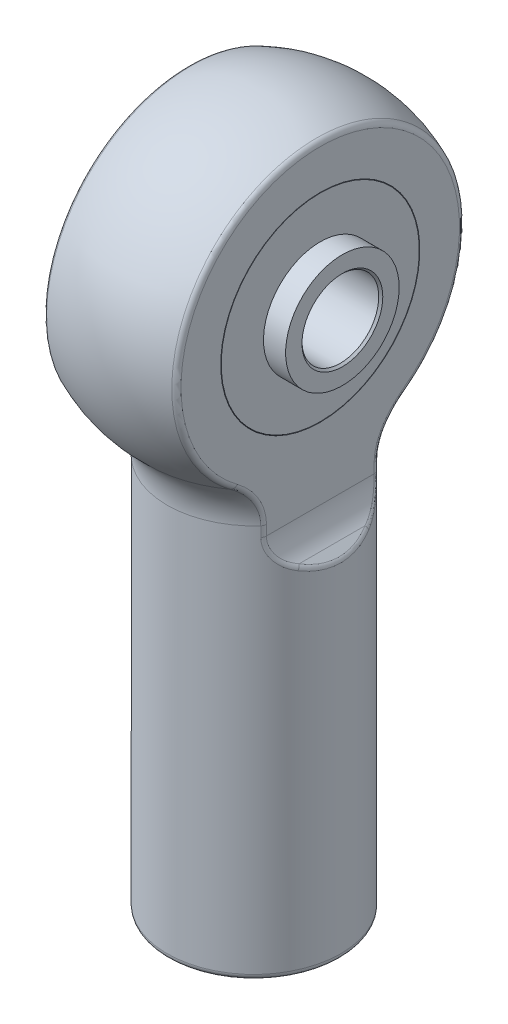
SolidWorks part; units mm, degrees
other "C-Rev Ball"
other "C-Rev Body"
material "AISI 1020"
ref_plane "Front Plane" through (0, 0, 0) normal (0, 0, 1) x (1, 0, 0)
ref_plane "Top Plane" through (0, 0, 0) normal (0, 1, 0) x (1, 0, 0)
ref_plane "Right Plane" through (0, 0, 0) normal (1, 0, 0) x (0, 0, -1)
sketch "Sketch1" plane through (0, 0, 0) normal (0, 0, 1) x (1, 0, 0)
  line L0 (0, 0) -> (0, -34.925) construction
  line L1 (-3.4544, -34.925) -> (-5.461, -34.925)
  line L2 (-5.461, -34.925) -> (-5.461, -8.28)
  line L3 (0, -10.8633) -> (0, 9.9187)
  line L4 (0, -10.8633) -> (-3.4544, -12.7)
  line L5 (-3.4544, -12.7) -> (-3.4544, -34.925)
  arc A0 (0, 9.9187) -> (-5.461, -8.28) centre (0, 0) ccw
  dimension "D2" = 19.8374
  dimension "D1" = 34.925
  dimension "D3" = 10.922
  dimension "D4" = 22.225
  dimension "D7" = 118
  dimension "D8" = 6.9088
revolve "Revolve1" add sketch "Sketch1" angle 360 about L0
sketch "Sketch2" plane through (0, 0, 0) normal (0, 0, 1) x (1, 0, 0)
  line L0 (0, 0) -> (0, 10.8779) construction
  line L1 (4.1656, 9.0016) -> (4.1656, -10.7585)
  line L2 (-4.1656, 9.0016) -> (-4.1656, -10.7585)
  line L4 (-4.9095, -12.5545) -> (-5.461, -13.106)
  line L5 (-5.461, -8.28) -> (-5.461, -34.925) construction
  line L6 (-5.461, -8.28) -> (-5.461, -13.106)
  line L7 (4.9095, -12.5545) -> (5.461, -13.106)
  line L8 (5.461, -8.28) -> (5.461, -13.106)
  arc A0 (5.461, -8.28) -> (-5.461, -8.28) centre (0, 0) ccw construction
  arc A1 (5.461, -8.28) -> (4.1656, 9.0016) centre (0, 0) ccw
  arc A2 (-4.1656, 9.0016) -> (-5.461, -8.28) centre (0, 0) ccw
  arc A3 (4.1656, -10.7585) -> (4.9095, -12.5545) centre (6.7056, -10.7585) ccw
  arc A4 (-4.1656, -10.7585) -> (-4.9095, -12.5545) centre (-6.7056, -10.7585) cw
  point P10 (4.1656, -11.8106)
  point P17 (-4.1656, -11.8106)
  dimension "D4" = 2.54
  dimension "D1" = 8.3312
  dimension "D2" = 45
  dimension "D3" = 4.826
extrude "Extrude1" cut sketch "Sketch2" against normal through all and the other way through all
sketch "Sketch3" plane through (4.1656, 0, 0) normal (1, 0, 0) x (0, 0, -1)
  circle A0 centre (0, 0) radius 3.5687
  dimension "D1" = 7.1374
extrude "Extrude2" add sketch "Sketch3" against normal offset from surface 5.5562 and the other way offset from surface (1.3906 mm away) 5.5562 up to plane "Right Plane" offset beyond the face yes other way up to plane "Right Plane"
hole_wizard "#11 (0.191) Diameter Hole1" positions "Sketch5" profile "Sketch4" hole size "#11" standard "Ansi Inch" end condition through all
sketch "Sketch5" plane through (5.5562, 0, 0) normal (1, 0, 0) x (0, 0, -1)
  point P0 (0, 0)
sketch "Sketch4" plane through (5.5562, 0, 0) normal (0, 1, 0) x (0, 0, -1)
  line L0 (0, 0) -> (0, 11.1125)
  line L1 (0, 11.1125) -> (2.54, 11.1125)
  line L2 (2.413, 10.9855) -> (2.413, 0.127)
  line L3 (2.413, 0.127) -> (2.54, 0)
  line L5 (2.54, 0) -> (0, 0)
  line L6 (-2.413, 0.127) -> (-2.54, 0) construction
  line L7 (2.54, 11.1125) -> (2.413, 10.9855)
  line L8 (-2.54, 11.1125) -> (-2.413, 10.9855) construction
  line L11 (0, -6.35) -> (0, 107.95) construction
  dimension "Thru Hole Dia." = 4.826
  dimension "Thru Hole Depth" = 11.1125
  dimension "Near C'Sink Dia." = 5.08
  dimension "Near C'Sink Angle" = 90
  dimension "Far C'Sink Dia." = 5.08
  dimension "Far C'Sink Angle" = 90
fillet "Fillet2" radius 3.81 2 edges at (0, -8.28, -5.461) (0, -8.28, 5.461)
fillet "Fillet1" radius 0.381 17 edges at (4.1656, -10.442, 3.5313) (4.1656, -10.442, -3.5313) (4.5846, -12.156, -2.9671) (4.3234, -11.6398, 3.3363) (5.461, -13.106, 0) (-4.1656, -10.442, -3.5313) (-4.1656, -10.442, 3.5313) (-4.5846, -12.156, 2.9671) (-4.3234, -11.6398, -3.3363) (-5.461, -13.106, 0) (-4.1656, 9.0016, 0) (4.1656, 9.0016, 0) (-5.461, -34.925, 0) (-4.1656, -9.1205, 3.7366) (-4.1656, -8.3829, -4.154) (4.1656, -9.1205, -3.7366) (4.1656, -8.3829, 4.154)
sketch "Sketch6" plane through (0, 0, 0) normal (1, 0, 0) x (0, 0, -1)
  line L0 (-11.8595, 0) -> (11.8595, 0) construction
  line L1 (-7.5184, 0) -> (-7.493, 0)
  line L2 (7.493, 0) -> (7.5184, 0)
  arc A1 (7.493, 0) -> (-7.493, 0) centre (0, 0) ccw
  arc A2 (7.5184, 0) -> (-7.5184, 0) centre (0, 0) ccw
  circle A3 centre (0, 0) radius 7.493 construction
  circle A4 centre (0, 0) radius 7.5184 construction
  dimension "D1" = 14.986
  dimension "D2" = 0.0254
revolve "Cut-Revolve1" cut sketch "Sketch6" angle 360 about L2
